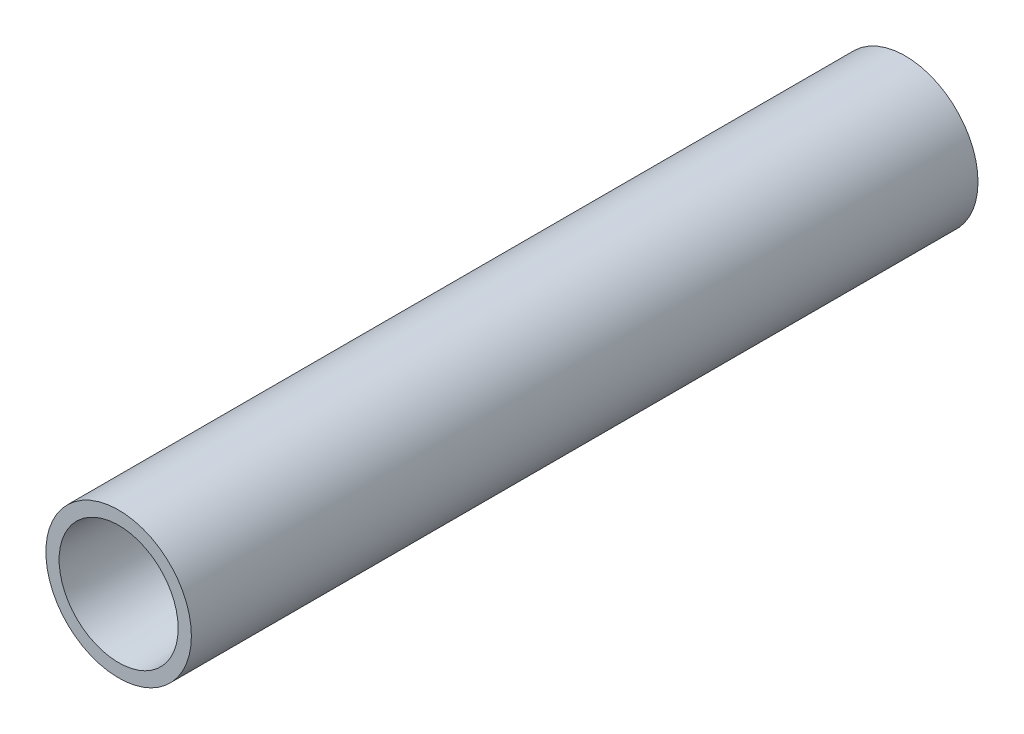
SolidWorks part; units mm, degrees
ref_plane "Front Plane" through (0, 0, 0) normal (0, 0, 1) x (1, 0, 0)
ref_plane "Top Plane" through (0, 0, 0) normal (0, 1, 0) x (1, 0, 0)
ref_plane "Right Plane" through (0, 0, 0) normal (1, 0, 0) x (0, 0, -1)
sketch "Sketch1" plane through (0, 0, 0) normal (0, 0, 1) x (1, 0, 0)
  circle A0 centre (0, 0) radius 2.775
  dimension "D1" = 5.55
extrude "Boss-Extrude1" add sketch "Sketch1" along normal blind 30
sketch "Sketch2" plane through (0, 0, 0) normal (0, 0, 1) x (1, 0, 0)
  circle A0 centre (0, 0) radius 2.27
  dimension "D1" = 4.54
extrude "Cut-Extrude1" cut sketch "Sketch2" along a picked direction on the side of the normal blind 5.68 draft 3.074
sketch "Sketch7" plane through (0, 0, 0) normal (0, 0, 1) x (1, 0, 0)
  circle A0 centre (0, 0) radius 1
extrude "Cut-Extrude2" cut sketch "Sketch7" along normal through all
sketch "Sketch9" plane through (0, 0, 30) normal (0, 0, 1) x (1, 0, 0)
  circle A0 centre (0, 0) radius 2.27
  circle A1 centre (0, 0) radius 2.27 construction
extrude "Cut-Extrude3" cut sketch "Sketch9" against normal blind 5.68 draft 3.074
